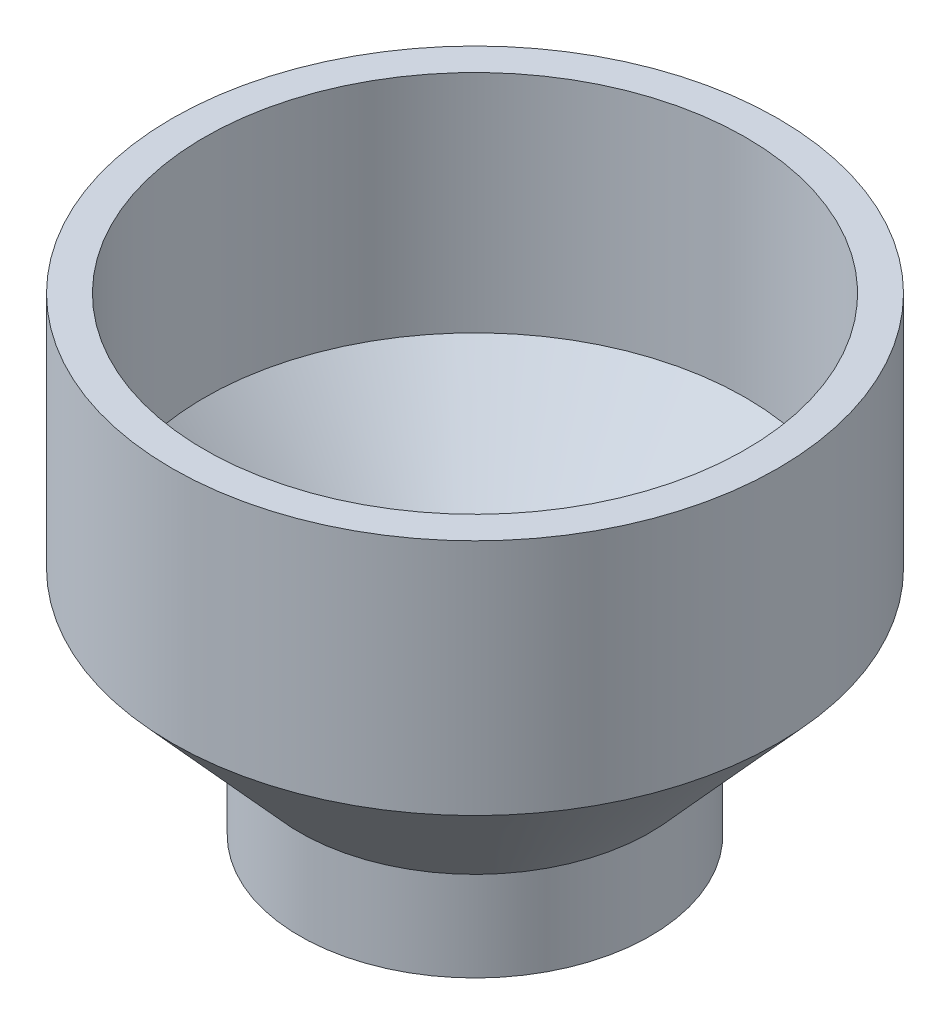
SolidWorks part; units mm, degrees
ref_plane "Front" through (0, 0, 0) normal (0, 0, 1) x (1, 0, 0)
ref_plane "Top" through (0, 0, 0) normal (0, 1, 0) x (1, 0, 0)
ref_plane "Right" through (0, 0, 0) normal (1, 0, 0) x (0, 0, -1)
sketch "Sketch1" plane through (0, 0, 0) normal (0, 0, 1) x (1, 0, 0)
  line L0 (-57.15, 0) -> (-57.15, -47.625)
  line L1 (-57.15, -47.625) -> (-30.1625, -77.47)
  line L2 (-30.1625, -77.47) -> (-30.1625, -99.06)
  line L3 (0, 0) -> (0, 25.492) construction
  point P6 (0, 0)
  dimension "D1" = 114.3
  dimension "D2" = 60.325
  dimension "D3" = 47.625
  dimension "D4" = 99.06
  dimension "D5" = 21.59
revolve "Revolve-Thin1" add sketch "Sketch1" angle 360 about L3
